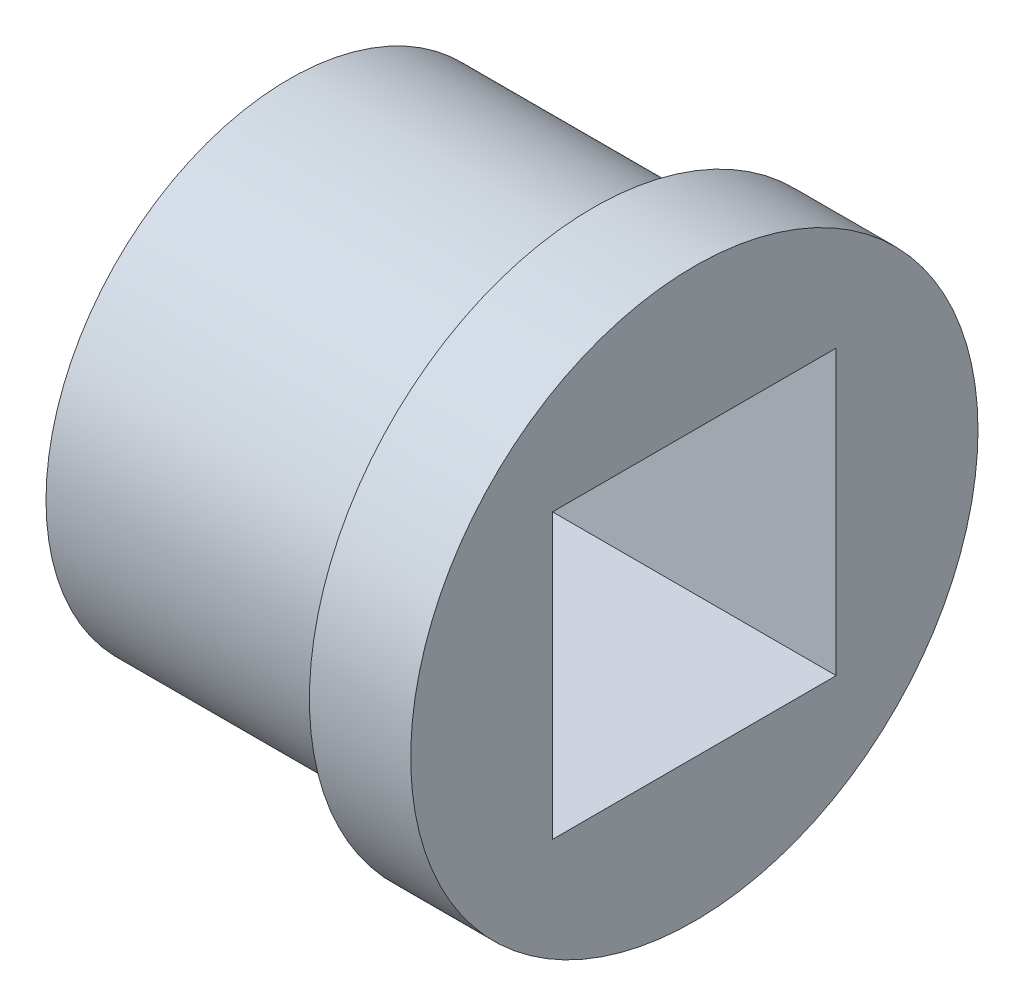
SolidWorks part; units mm, degrees
ref_plane "Front Plane" through (0, 0, 0) normal (0, 0, 1) x (1, 0, 0)
ref_plane "Top Plane" through (0, 0, 0) normal (0, 1, 0) x (1, 0, 0)
ref_plane "Right Plane" through (0, 0, 0) normal (1, 0, 0) x (0, 0, -1)
sketch "Sketch2" plane through (0, 0, 0) normal (1, 0, 0) x (0, 0, -1)
  circle A0 centre (0, 0) radius 3.048
  dimension "D2" = 6.096
extrude "Boss-Extrude1" add sketch "Sketch2" along normal blind 3.81
sketch "Sketch3" plane through (3.81, 0, 0) normal (1, 0, 0) x (0, 0, -1)
  circle A0 centre (0, 0) radius 3.556
  dimension "D1" = 7.112
extrude "Boss-Extrude2" add sketch "Sketch3" along normal blind 1.27
sketch "Sketch4" plane through (0, 0, 0) normal (-1, 0, 0) x (0, 0, 1)
  line L1 (1.778, 1.778) -> (-1.778, 1.778)
  line L2 (1.778, 1.778) -> (1.778, -1.778)
  line L3 (1.778, -1.778) -> (-1.778, -1.778)
  line L4 (-1.778, 1.778) -> (-1.778, -1.778)
  line L5 (1.778, 1.778) -> (-1.778, -1.778) construction
  line L6 (1.778, -1.778) -> (-1.778, 1.778) construction
  point P0 (0, 0)
  dimension "D1" = 3.556
extrude "Cut-Extrude1" cut sketch "Sketch4" against normal through all
